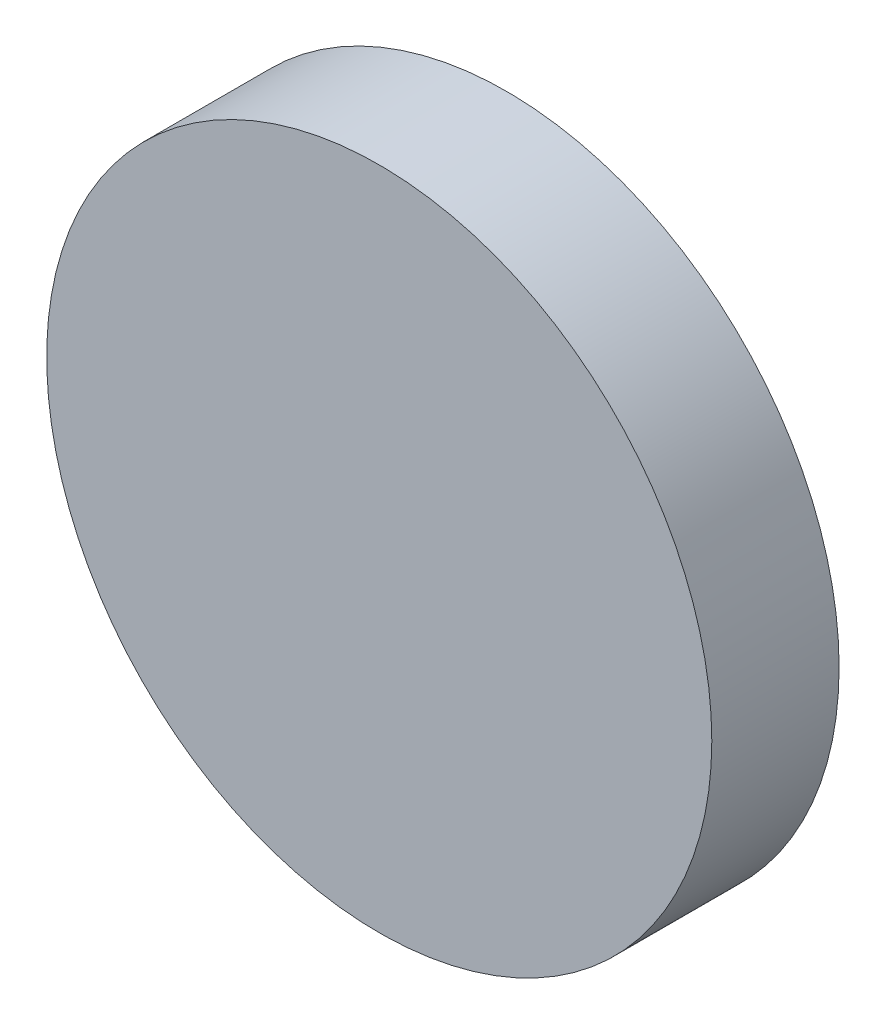
SolidWorks part; units mm, degrees
material "Bismuth"
ref_plane "Front" through (0, 0, 0) normal (0, 0, 1) x (1, 0, 0)
ref_plane "Top" through (0, 0, 0) normal (0, 1, 0) x (1, 0, 0)
ref_plane "Right" through (0, 0, 0) normal (1, 0, 0) x (0, 0, -1)
sketch "Sketch1" plane through (0, 0, 0) normal (0, 0, 1) x (1, 0, 0)
  circle A0 centre (0, 0) radius 128
extrude "Boss-Extrude1" add sketch "Sketch1" along normal blind 49
